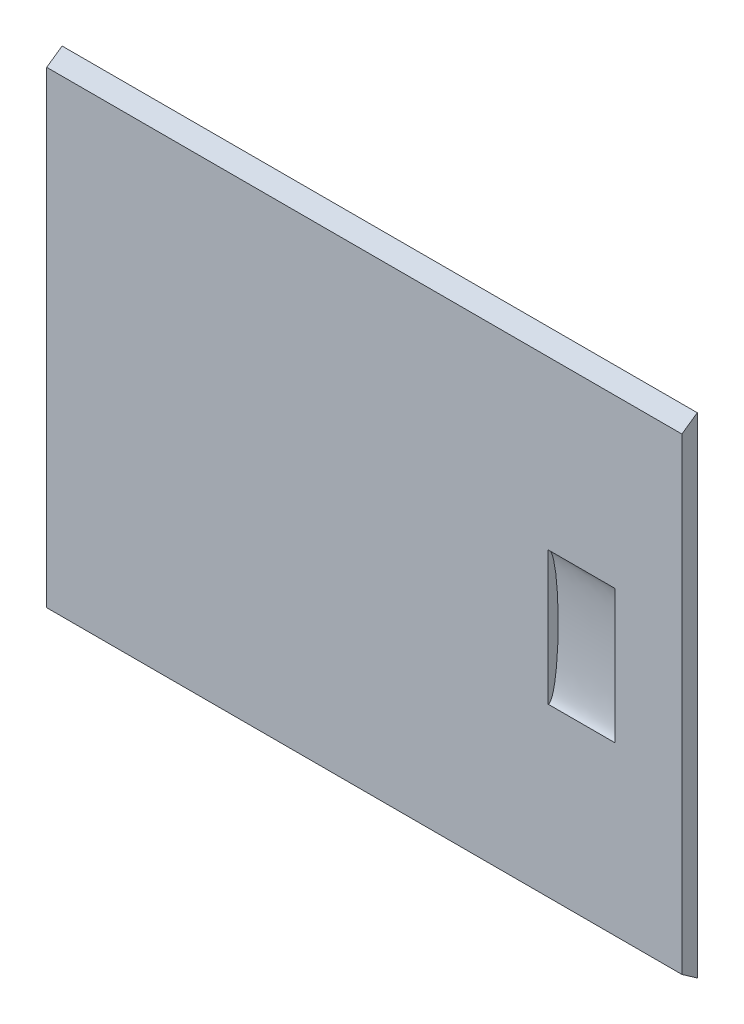
SolidWorks part; units mm, degrees
material "ABS"
ref_plane "Plano frontal" through (0, 0, 0) normal (0, 0, 1) x (1, 0, 0)
ref_plane "Plano superior" through (0, 0, 0) normal (0, 1, 0) x (1, 0, 0)
ref_plane "Plano direito" through (0, 0, 0) normal (1, 0, 0) x (0, 0, -1)
sketch "Esboço1" plane through (0, 0, 0) normal (1, 0, 0) x (0, 0, -1)
  line L0 (-13.8235, 0) -> (15.3418, 0) construction
  line L1 (2.3, -70) -> (-2.3, -70)
  line L2 (2.3, -70) -> (2.3, 70)
  line L3 (2.3, 70) -> (-2.3, 70)
  line L4 (-2.3, -70) -> (-2.3, 70)
  line L5 (2.3, -70) -> (-2.3, 70) construction
  line L6 (2.3, 70) -> (-2.3, -70) construction
  line L7 (-2.3, 70) -> (2.3, 73.221)
  line L8 (2.3, 70) -> (2.3, 73.221)
  line L9 (2.3, -70) -> (2.3, -73.221)
  line L10 (-2.3, -70) -> (2.3, -73.221)
  line L11 (2.3, -70) -> (-2.3, -70)
  point P0 (0, 0)
  dimension "D1" = 140
  dimension "D2" = 4.6
  dimension "D3" = 35
extrude "Ressalto-extrusão1" add sketch "Esboço1" along normal blind 190 contours L4 L1 L2 L3 | L3 L8 L7 | L1 L10 L9
sketch "Esboço2" plane through (190, 0, 0) normal (1, 0, 0) x (0, 0, -1)
  line L0 (-33.6064, 0) -> (32.2177, 0) construction
  line L1 (-2.3, -70) -> (-2.3, 70) construction
  ellipse E0 centre (-2.3, 0) end of major axis (-2.2438, -20) minor radius 3
  dimension "D1" = 6
  dimension "D2" = 40
extrude "Corte-extrusão1" cut sketch "Esboço2" against normal blind 20 from offset 20 offset against normal yes
